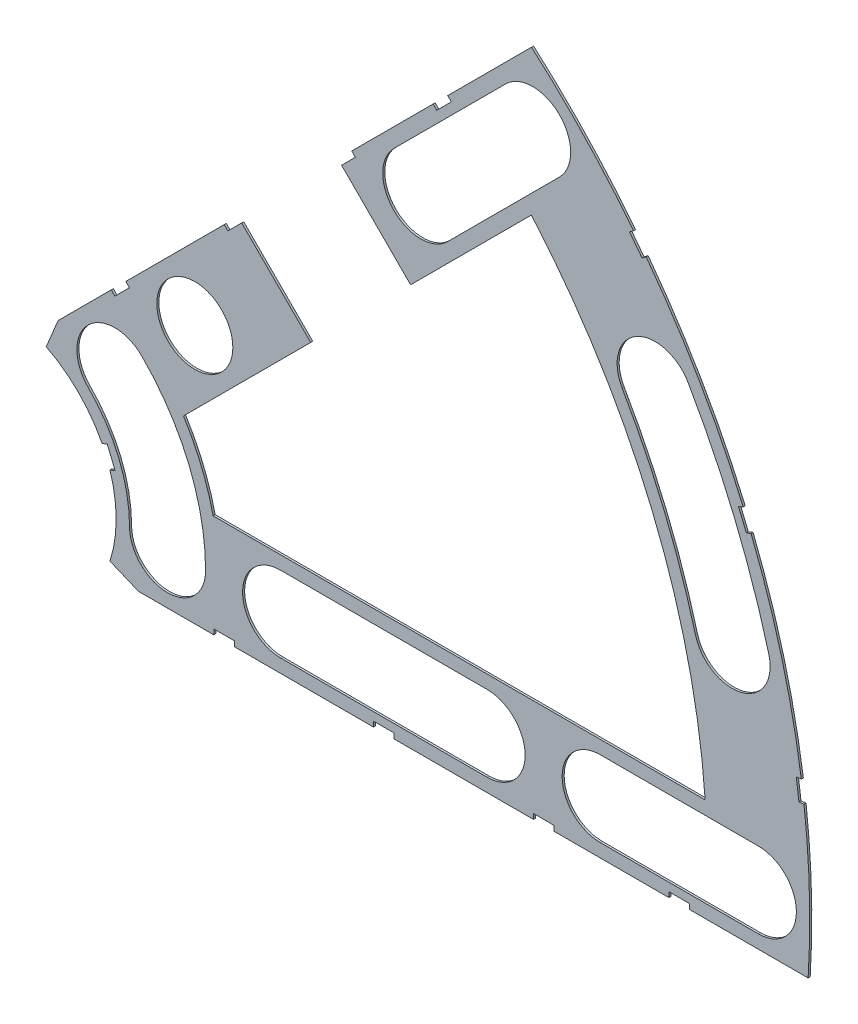
SolidWorks part; units mm, degrees
material "PTFE (general)"
ref_plane "Front Plane" through (0, 0, 0) normal (0, 0, 1) x (1, 0, 0)
ref_plane "Top Plane" through (0, 0, 0) normal (0, 1, 0) x (1, 0, 0)
ref_plane "Right Plane" through (0, 0, 0) normal (1, 0, 0) x (0, 0, -1)
sketch "Sketch1" plane through (0, 0, 0) normal (0, 0, 1) x (1, 0, 0)
  line L0 (0, 0) -> (320.3893, 0) construction
  line L1 (0, 0) -> (155.5285, 155.5285) construction
  line L2 (67.2115, 76.1917) -> (8.6967, 17.6769)
  line L3 (8.6967, 17.6769) -> (7.229, 14.1336)
  line L4 (101.4014, -6.35) -> (18.6489, -6.35)
  line L5 (15.1056, -4.8823) -> (18.6489, -6.35)
  line L6 (88.6729, 6.35) -> (27.8605, 6.35)
  line L9 (67.1914, 58.2111) -> (24.1905, 15.2102)
  line L10 (0, 0) -> (40.4486, 97.6516) construction
  line L11 (0, 0) -> (123.4567, -51.1374) construction
  line L18 (8.6967, 17.6769) -> (13.294, 8.6183) construction
  line L19 (18.6489, -6.35) -> (15.4943, 3.3063) construction
  line L20 (27.8605, 6.35) -> (27.7442, 6.7059) construction
  line L21 (24.1905, 15.2102) -> (24.3599, 14.8764) construction
  arc A0 (7.229, 14.1336) -> (15.1056, -4.8823) centre (0, 0) cw
  arc A1 (67.2115, 76.1917) -> (101.4014, -6.35) centre (0, 0) cw
  arc A2 (24.1905, 15.2102) -> (27.8605, 6.35) centre (0, 0) cw
  arc A3 (67.1914, 58.2111) -> (88.6729, 6.35) centre (0, 0) cw
  arc A8 (13.294, 8.6183) -> (15.4943, 3.3063) centre (0, 0) cw construction
  arc A9 (24.3599, 14.8764) -> (27.7442, 6.7059) centre (0, 0) cw construction
  dimension "D1" = 45
  dimension "D3" = 6.35
  dimension "D4" = 15.875
  dimension "D7" = 22.5
  dimension "D8" = 101.6
  dimension "D11" = 12.7
  dimension "D12" = 12.7
  dimension "D2" = 6.35
  dimension "D5" = 67.5
  dimension "D9" = 1.27
  dimension "D10" = 1.27
  dimension "D6" = 12.7
extrude "Boss-Extrude1" add sketch "Sketch1" along normal blind 0.254
sketch "Sketch2" plane through (0, 0, 0.254) normal (0, 0, 1) x (1, 0, 0)
  line L0 (0, 0) -> (101.6, 0) construction
  line L1 (0, 0) -> (71.842, 71.842) construction
  line L3 (0, 0) -> (22.225, 0) construction
  line L4 (0, 0) -> (15.7154, 15.7154) construction
  line L5 (0, 0) -> (95.25, 0) construction
  line L6 (0, 0) -> (92.0044, 24.6525) construction
  arc A0 (101.4014, -6.35) -> (67.2115, 76.1917) centre (0, 0) ccw construction
  circle A1 centre (22.225, 0) radius 4.699
  arc A2 (15.1056, -4.8823) -> (7.229, 14.1336) centre (0, 0) ccw construction
  circle A3 centre (36.195, 0) radius 4.699
  circle A4 centre (61.722, 0) radius 4.699
  circle A5 centre (75.692, 0) radius 4.699
  circle A6 centre (95.25, 0) radius 4.699
  circle A7 centre (15.7154, 15.7154) radius 4.699
  circle A8 centre (25.5937, 25.5937) radius 4.699
  circle A9 centre (43.644, 43.644) radius 4.699
  circle A10 centre (53.5223, 53.5223) radius 4.699
  circle A11 centre (92.0044, 24.6525) radius 4.699
  circle A12 centre (82.4889, 47.625) radius 4.699
  circle A13 centre (67.3519, 67.3519) radius 4.699
  dimension "D3" = 9.398
  dimension "D1" = 45
  dimension "D2" = 6.35
  dimension "D4" = 6.35
  dimension "D5" = 13.97
  dimension "D7" = 13.97
  dimension "D8" = 19.558
  dimension "D9" = 45
  dimension "D10" = 15
  dimension "D11" = 25.527
  dimension "D6" = 2
extrude "Cut-Extrude1" cut sketch "Sketch2" against normal through all
sketch "Sketch3" plane through (0, 0, 0.254) normal (0, 0, 1) x (1, 0, 0)
  line L0 (15.2664, 24.2467) -> (17.0625, 26.0427)
  line L1 (15.2664, 24.2467) -> (15.7154, 23.7977)
  line L2 (17.0625, 26.0427) -> (17.5115, 25.5937)
  line L3 (15.7154, 23.7977) -> (17.5115, 25.5937)
  line L4 (67.2115, 76.1917) -> (8.6967, 17.6769) construction
  line L5 (44.9911, 53.9713) -> (43.195, 52.1753)
  line L6 (44.9911, 53.9713) -> (45.4401, 53.5223)
  line L7 (43.195, 52.1753) -> (43.644, 51.7263)
  line L8 (45.4401, 53.5223) -> (43.644, 51.7263)
  line L9 (27.94, -6.35) -> (30.48, -6.35)
  line L10 (27.94, -6.35) -> (27.94, -5.715)
  line L11 (30.48, -6.35) -> (30.48, -5.715)
  line L12 (27.94, -5.715) -> (30.48, -5.715)
  line L13 (18.6489, -6.35) -> (101.4014, -6.35) construction
  line L14 (67.437, -6.35) -> (69.977, -6.35)
  line L15 (67.437, -6.35) -> (67.437, -5.715)
  line L16 (69.977, -6.35) -> (69.977, -5.715)
  line L17 (67.437, -5.715) -> (69.977, -5.715)
  line L18 (29.2307, 38.211) -> (31.0268, 40.007)
  line L19 (29.2307, 38.211) -> (29.6797, 37.762)
  line L20 (31.0268, 40.007) -> (31.4758, 39.558)
  line L21 (29.6797, 37.762) -> (31.4758, 39.558)
  line L22 (56.845, 65.8253) -> (55.049, 64.0292)
  line L23 (56.845, 65.8253) -> (57.294, 65.3763)
  line L24 (55.049, 64.0292) -> (55.498, 63.5802)
  line L25 (57.294, 65.3763) -> (55.498, 63.5802)
  line L26 (47.6885, -6.35) -> (50.2285, -6.35)
  line L27 (47.6885, -6.35) -> (47.6885, -5.715)
  line L28 (50.2285, -6.35) -> (50.2285, -5.715)
  line L29 (47.6885, -5.715) -> (50.2285, -5.715)
  line L30 (84.201, -6.35) -> (86.741, -6.35)
  line L31 (84.201, -6.35) -> (84.201, -5.715)
  line L32 (86.741, -6.35) -> (86.741, -5.715)
  line L33 (84.201, -5.715) -> (86.741, -5.715)
  line L34 (0, 0) -> (100.7308, 13.2615) construction
  line L35 (0, 0) -> (93.8662, 38.8806) construction
  line L36 (0, 0) -> (80.6047, 61.8502) construction
  line L37 (0, 0) -> (101.6, 0) construction
  line L38 (99.9355, 14.4377) -> (100.267, 11.9194)
  line L39 (99.9355, 14.4377) -> (101.1946, 14.6035)
  line L40 (100.267, 11.9194) -> (101.5261, 12.0852)
  line L41 (101.1946, 14.6035) -> (101.5261, 12.0852)
  line L42 (99.9355, 14.4377) -> (101.5261, 12.0852) construction
  line L43 (100.267, 11.9194) -> (101.1946, 14.6035) construction
  line L44 (93.7655, 37.4643) -> (94.9388, 37.9503)
  line L45 (93.7655, 37.4643) -> (92.7935, 39.811)
  line L46 (94.9388, 37.9503) -> (93.9668, 40.297)
  line L47 (92.7935, 39.811) -> (93.9668, 40.297)
  line L48 (93.7655, 37.4643) -> (93.9668, 40.297) construction
  line L49 (94.9388, 37.9503) -> (92.7935, 39.811) construction
  line L50 (79.3278, 62.4712) -> (80.874, 60.456)
  line L51 (79.3278, 62.4712) -> (80.3354, 63.2443)
  line L52 (80.874, 60.456) -> (81.8816, 61.2292)
  line L53 (80.3354, 63.2443) -> (81.8816, 61.2292)
  line L54 (79.3278, 62.4712) -> (81.8816, 61.2292) construction
  line L55 (80.874, 60.456) -> (80.3354, 63.2443) construction
  line L56 (13.5939, 7.0054) -> (14.5659, 4.6588)
  line L57 (13.5939, 7.0054) -> (14.7672, 7.4914)
  line L58 (14.5659, 4.6588) -> (15.7393, 5.1448)
  line L59 (14.7672, 7.4914) -> (15.7393, 5.1448)
  line L60 (13.5939, 7.0054) -> (15.7393, 5.1448) construction
  line L61 (14.5659, 4.6588) -> (14.7672, 7.4914) construction
  circle A0 centre (15.7154, 15.7154) radius 4.699 construction
  circle A1 centre (43.644, 43.644) radius 4.699 construction
  circle A2 centre (22.225, 0) radius 4.699 construction
  circle A3 centre (61.722, 0) radius 4.699 construction
  arc A4 (101.4014, -6.35) -> (67.2115, 76.1917) centre (0, 0) ccw construction
  arc A9 (15.1056, -4.8823) -> (7.229, 14.1336) centre (0, 0) ccw construction
  circle A10 centre (36.195, 0) radius 4.699 construction
  circle A11 centre (75.692, 0) radius 4.699 construction
  circle A12 centre (25.5937, 25.5937) radius 4.699 construction
  circle A13 centre (53.5223, 53.5223) radius 4.699 construction
  point P75 (14.6666, 6.0751)
  dimension "D2" = 5.715
  dimension "D3" = 2.54
  dimension "D6" = 5.715
  dimension "D8" = 0.635
  dimension "D9" = 5.715
  dimension "D12" = 5.715
  dimension "D4" = 7.5
  dimension "D5" = 22.5
  dimension "D7" = 37.5
  dimension "D10" = 90
  dimension "D11" = 1.27
  dimension "D14" = 0.635
  dimension "D15" = 90
  dimension "D18" = 0.635
  dimension "D19" = 90
  dimension "D22" = 0.635
  dimension "D20" = 1.27
  dimension "D17" = 0.635
  dimension "D13" = 11.4935
  dimension "D16" = 8.509
  dimension "D21" = 11.4935
  dimension "D23" = 8.509
extrude "Cut-Extrude2" cut sketch "Sketch3" against normal through all
sketch "Sketch5" plane through (0, 0, 0.254) normal (0, 0, 1) x (1, 0, 0)
  line L0 (30.039, 40.8153) -> (42.3868, 53.1631)
  line L1 (30.039, 40.8153) -> (40.8153, 30.039)
  line L2 (42.3868, 53.1631) -> (53.1631, 42.3868)
  line L3 (45.4401, 53.5223) -> (44.9911, 53.9713) construction
  line L4 (40.8153, 30.039) -> (53.1631, 42.3868)
  line L8 (43.195, 52.1753) -> (31.0268, 40.007) construction
  line L10 (29.2307, 38.211) -> (29.6797, 37.762) construction
  dimension "D1" = 15.24
  dimension "D2" = 1.27
  dimension "D3" = 2.413
  dimension "D4" = 2.413
sketch "Sketch6" plane through (0, 0, 0.254) normal (0, 0, 1) x (1, 0, 0)
  line L0 (0, 0) -> (101.6, 0) construction
  line L1 (0, 0) -> (71.842, 71.842) construction
  line L2 (0, 0) -> (87.9882, 50.8) construction
  line L3 (0, 0) -> (98.1381, 26.296) construction
  line L7 (53.5223, 53.5223) -> (67.3519, 67.3519) construction
  line L8 (50.1996, 56.845) -> (64.0292, 70.6746)
  line L9 (56.845, 50.1996) -> (70.6746, 64.0292)
  line L10 (61.722, 0) -> (36.195, 0) construction
  line L11 (61.722, -4.699) -> (36.195, -4.699)
  line L12 (61.722, 4.699) -> (36.195, 4.699)
  line L13 (95.25, 0) -> (75.692, 0) construction
  line L14 (95.25, -4.699) -> (75.692, -4.699)
  line L15 (95.25, 4.699) -> (75.692, 4.699)
  arc A0 (79.8253, 62.8529) -> (67.2115, 76.1917) centre (0, 0) ccw construction
  arc A1 (15.7154, 15.7154) -> (22.225, 0) centre (0, 0) cw construction
  arc A2 (26.924, 0) -> (19.0381, 19.0381) centre (0, 0) ccw
  arc A3 (17.526, 0) -> (12.3928, 12.3928) centre (0, 0) ccw
  arc A4 (17.526, 0) -> (26.924, 0) centre (22.225, 0) ccw
  arc A5 (101.4014, -6.35) -> (100.8887, 12.0013) centre (0, 0) ccw construction
  arc A6 (19.0381, 19.0381) -> (12.3928, 12.3928) centre (15.7154, 15.7154) ccw
  arc A7 (93.3728, 40.0509) -> (81.3715, 60.8378) centre (0, 0) ccw construction
  arc A8 (100.5572, 14.5196) -> (94.3448, 37.7043) centre (0, 0) ccw construction
  arc A9 (82.4889, 47.625) -> (92.0044, 24.6525) centre (0, 0) cw construction
  arc A10 (96.5433, 25.8687) -> (86.5584, 49.9745) centre (0, 0) ccw
  arc A11 (87.4655, 23.4363) -> (78.4195, 45.2755) centre (0, 0) ccw
  arc A12 (87.4655, 23.4363) -> (96.5433, 25.8687) centre (92.0044, 24.6525) ccw
  arc A13 (86.5584, 49.9745) -> (78.4195, 45.2755) centre (82.4889, 47.625) ccw
  circle A14 centre (67.3519, 67.3519) radius 4.699 construction
  arc A16 (50.1996, 56.845) -> (56.845, 50.1996) centre (53.5223, 53.5223) ccw
  arc A17 (70.6746, 64.0292) -> (64.0292, 70.6746) centre (67.3519, 67.3519) ccw
  arc A18 (61.722, -4.699) -> (61.722, 4.699) centre (61.722, 0) ccw
  arc A19 (36.195, 4.699) -> (36.195, -4.699) centre (36.195, 0) ccw
  arc A20 (95.25, -4.699) -> (95.25, 4.699) centre (95.25, 0) ccw
  arc A21 (75.692, 4.699) -> (75.692, -4.699) centre (75.692, 0) ccw
  point P8 (20.5332, 8.5051)
  point P12 (87.9995, 36.4506)
  point P48 (60.4371, 60.4371)
  point P59 (48.9585, 0)
  point P70 (85.471, 0)
  dimension "D2" = 9.398
  dimension "D5" = 9.398
  dimension "D1" = 45
  dimension "D3" = 9.398
  dimension "D4" = 9.398
extrude "Cut-Extrude4" cut sketch "Sketch6" against normal through all
extrude "Cut-Extrude5" cut sketch "Sketch5" against normal through all
equation "\"cSep\"= 1.005"
equation "\"D11@Sketch2\"=\"cSep\""
equation "\"cSep2\"= \"D8@Sketch2\""
equation "\"D13@Sketch3\"=\"cSep\"/2-.05"
equation "\"D16@Sketch3\"=\"cSep2\"/2-.05"
equation "\"D21@Sketch3\"=\"cSep\"/2-.05"
equation "\"D23@Sketch3\"=\"cSep2\"/2-.05"
